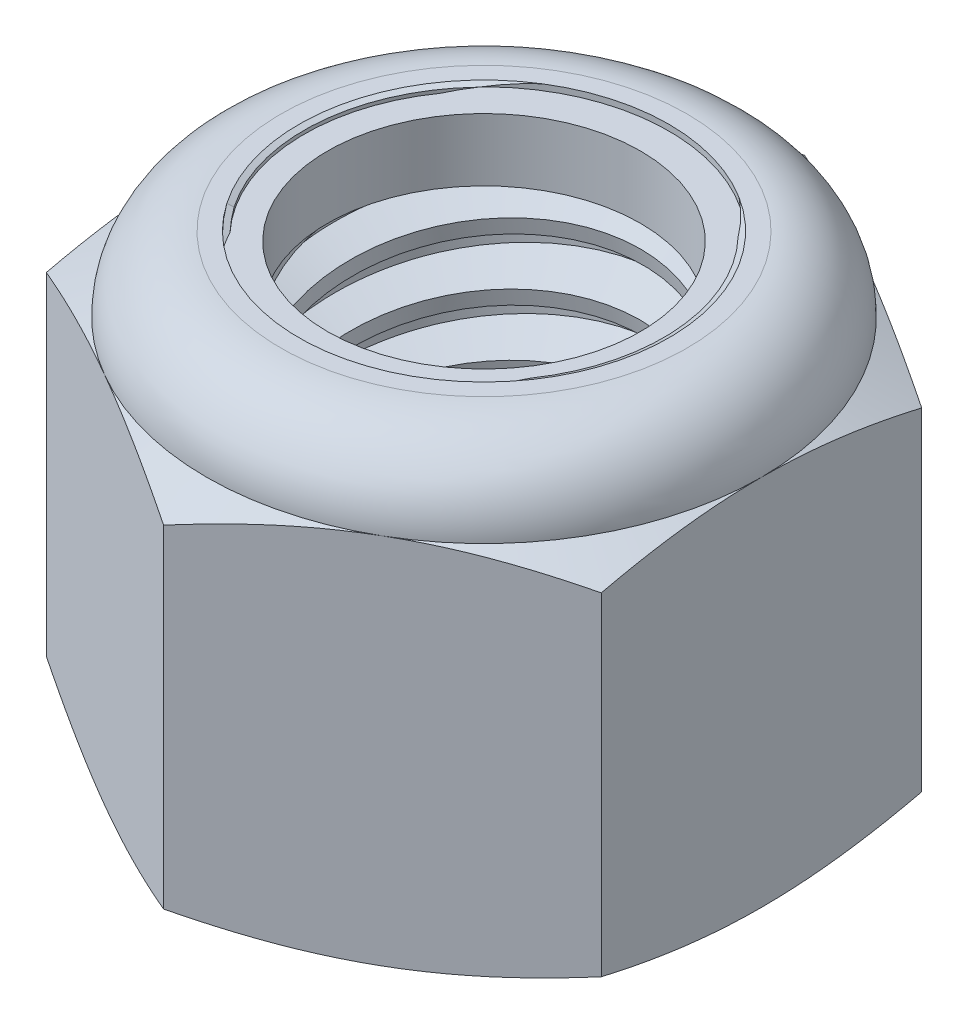
SolidWorks part; units mm, degrees
ref_plane "Front" through (0, 0, 0) normal (0, 0, 1) x (1, 0, 0)
ref_plane "Top" through (0, 0, 0) normal (0, 1, 0) x (1, 0, 0)
ref_plane "Right" through (0, 0, 0) normal (1, 0, 0) x (0, 0, -1)
sketch "Sketch1" plane through (0, 0, 0) normal (0, 1, 0) x (1, 0, 0)
  line L1 (0, 8.2489) -> (-7.1438, 4.1244)
  line L2 (-7.1438, 4.1244) -> (-7.1438, -4.1244)
  line L3 (-7.1438, -4.1244) -> (0, -8.2489)
  line L4 (0, -8.2489) -> (7.1437, -4.1244)
  line L5 (7.1437, -4.1244) -> (7.1437, 4.1244)
  line L6 (7.1437, 4.1244) -> (0, 8.2489)
  circle A0 centre (0, 0) radius 7.1438 construction
  dimension "Hex Flats" = 14.2875
extrude "Extrude1" add sketch "Sketch1" along normal blind 11.5094
sketch "Sketch2" plane through (0, 0, 0) normal (1, 0, 0) x (0, 0, -1)
  line L0 (-4.7625, 0) -> (-4.7625, 11.5094) construction
  line L1 (0, 0) -> (4.7625, 0)
  line L2 (0, 0) -> (0, 11.5094)
  line L3 (0, 11.5094) -> (4.7625, 11.5094)
  line L4 (4.7625, 0) -> (4.7625, 11.5094)
  line L5 (-4.1244, 11.5094) -> (4.1244, 11.5094) construction
  line L7 (0, -4.7625) -> (0, 0) construction
  dimension "Thread Dia" = 9.525
revolve "Revolve1" add sketch "Sketch2" angle 360 about L7
sketch "Sketch3" plane through (0, 0, 0) normal (1, 0, 0) x (0, 0, -1)
  line L0 (4.7625, 11.5094) -> (-4.7625, 11.5094) construction
  line L1 (-4.7625, 11.5094) -> (-4.7625, 9.9219) construction
  line L2 (-4.7625, 9.9219) -> (4.7625, 11.5094) construction
  line L3 (4.7625, 11.5094) -> (4.7951, 11.3136) construction
  line L4 (4.7951, 11.3136) -> (5.0235, 9.9435)
  line L5 (5.0235, 9.9435) -> (4.0944, 10.2916)
  line L6 (4.0944, 10.2916) -> (4.0291, 10.683)
  line L7 (4.0291, 10.683) -> (4.7951, 11.3136)
  line L8 (4.0617, 10.4873) -> (4.9093, 10.6286) construction
  line L9 (4.7625, 11.5094) -> (4.7625, 10.6041) construction
  line L10 (4.7625, 10.6041) -> (-4.7625, 9.0166) construction
  line L11 (-4.7625, 9.0166) -> (-4.7625, 9.9219) construction
  line L12 (-0.2832, 11.5094) -> (0.2832, 8.1113) construction
  line L13 (-4.7625, 0) -> (-4.7625, 11.5094) construction
  line L14 (0, 11.5094) -> (4.7625, 11.5094) construction
  line L15 (4.7625, 0) -> (4.7625, 11.5094) construction
  point P13 (0, 9.8103)
  dimension "D1" = 0.1984
  dimension "D2" = 0.3969
  dimension "Thread Pitch" = 1.5875
  dimension "D4" = 60
  dimension "D5" = 1.5875
revolve "Cut-Revolve1" cut sketch "Sketch3" angle 360 about L12
pattern_linear "LPattern1" count 7 spacing 1.5875 along (0, -1, 0) count 2 spacing 1.5875 along (0, 1, 0) of "Cut-Revolve1"
sketch "Sketch4" plane through (0, 0, 0) normal (1, 0, 0) x (0, 0, -1)
  line L0 (0, 11.5094) -> (4.7625, 11.5094)
  line L1 (4.7625, 11.5094) -> (4.0291, 11.1674)
  line L2 (4.0291, 11.1674) -> (4.0291, 0.342)
  line L3 (4.0291, 0.342) -> (4.7625, 0)
  line L4 (4.7625, 0) -> (0, 0)
  line L5 (0, 0) -> (0, 11.5094)
  line L6 (4.7625, 0) -> (4.7625, 11.5094) construction
  line L7 (0, 11.5094) -> (4.7625, 11.5094) construction
  line L8 (0, 0) -> (4.7625, 0) construction
  line L9 (0, 0) -> (0, 11.5094) construction
  line L10 (0, 11.5094) -> (0, 12.3186) construction
  dimension "D1" = 25
revolve "Cut-Revolve2" cut sketch "Sketch4" angle 360 about L10
combine bodies "Combine1" operation type subtract main body 112 bodies to subtract 111
sketch "Sketch5" plane through (0, 0, 0) normal (1, 0, 0) x (0, 0, -1)
  line L0 (0, 0) -> (7.1438, 0)
  line L1 (7.1438, 0) -> (8.2489, 0.5153)
  line L2 (8.2489, 0.5153) -> (8.2489, 9.0758)
  line L3 (8.2489, 9.0758) -> (7.1438, 9.5911)
  line L4 (5.2255, 11.5094) -> (5.2255, 12.7794)
  line L5 (5.2255, 12.7794) -> (9.5189, 12.7794)
  line L6 (9.5189, 12.7794) -> (9.5189, -1.27)
  line L7 (9.5189, -1.27) -> (0, -1.27)
  line L8 (0, -1.27) -> (0, 0)
  line L9 (7.1438, 9.5911) -> (7.1438, 0) construction
  line L10 (0, 0) -> (4.7625, 0) construction
  line L13 (8.2489, 4.7956) -> (9.5189, 4.7956) construction
  line L14 (8.2489, 11.5094) -> (8.2489, 0) construction
  line L15 (0, 0) -> (0, 12.7794) construction
  line L20 (0, 12.7794) -> (5.2255, 12.7794) construction
  line L22 (0, 11.5094) -> (4.7625, 11.5094) construction
  arc A0 (7.1438, 9.5911) -> (5.2255, 11.5094) centre (5.2255, 9.5911) ccw
  dimension "D1" = 25
  dimension "D2" = 1.27
  dimension "D3" = 11.5094
  dimension "D4" = 1.9182
revolve "Cut-Revolve3" cut sketch "Sketch5" angle 360 about L15
sketch "Sketch6" plane through (0, 0, 0) normal (1, 0, 0) x (0, 0, -1)
  line L0 (0, 9.5911) -> (6.9914, 9.5911)
  line L1 (5.2255, 11.357) -> (4.6273, 11.357)
  line L2 (0, 12.7794) -> (0, 9.5911)
  line L3 (4.6273, 12.7794) -> (0, 12.7794)
  line L4 (0, 12.7794) -> (5.2255, 12.7794) construction
  line L5 (0, 0) -> (0, 12.7794) construction
  line L6 (0, 12.7794) -> (0, 44.323) construction
  line L7 (4.6273, 11.357) -> (4.6273, 12.7794)
  line L8 (5.2255, 11.5094) -> (5.2255, 11.357) construction
  line L9 (4.6273, 11.357) -> (4.0291, 11.357) construction
  line L10 (4.0291, 11.357) -> (4.0291, 11.1674) construction
  arc A0 (6.9914, 9.5911) -> (5.2255, 11.357) centre (5.2255, 9.5911) ccw
  arc A1 (7.1438, 9.5911) -> (5.2255, 11.5094) centre (5.2255, 9.5911) ccw construction
  dimension "D1" = 0.1524
revolve "Cut-Revolve4" cut sketch "Sketch6" angle 360 about L6
sketch "Sketch7" plane through (0, 0, 0) normal (1, 0, 0) x (0, 0, -1)
  line L0 (4.0291, 9.6673) -> (6.9134, 9.6673)
  line L1 (5.2255, 11.2808) -> (4.0291, 11.2808)
  line L2 (4.0291, 11.2808) -> (4.0291, 9.6673)
  line L3 (4.0291, 9.6673) -> (0, 9.6673) construction
  line L4 (0, 9.6673) -> (0, 11.2808) construction
  line L5 (0, 11.2808) -> (4.0291, 11.2808) construction
  line L6 (4.0291, 9.6673) -> (4.0291, 9.5911) construction
  line L7 (0, 9.5911) -> (6.9914, 9.5911) construction
  line L8 (5.2255, 11.2808) -> (5.2255, 11.357) construction
  arc A0 (6.9134, 9.6673) -> (5.2255, 11.2808) centre (5.2255, 9.5911) ccw
  arc A2 (6.9914, 9.5911) -> (5.2255, 11.357) centre (5.2255, 9.5911) ccw construction
  dimension "D1" = 0.0762
revolve "Revolve2" add sketch "Sketch7" angle 360 about L4
equation "\"D1@Sketch3\"=\"Thread Pitch@Sketch3\"/8"
equation "\"D2@Sketch3\"=\"Thread Pitch@Sketch3\"/4"
equation "\"D5@Sketch3\"=\"Thread Pitch@Sketch3\""
equation "\"D4@LPattern1\"=\"Thread Pitch@Sketch3\""
equation "\"D3@LPattern1\"=\"Thread Pitch@Sketch3\""
equation "\"D1@LPattern1\"=\"Height@Extrude1\"/\"Thread Pitch@Sketch3\""
equation "\"D4@Sketch5\"=\"Height@Extrude1\"/6"
